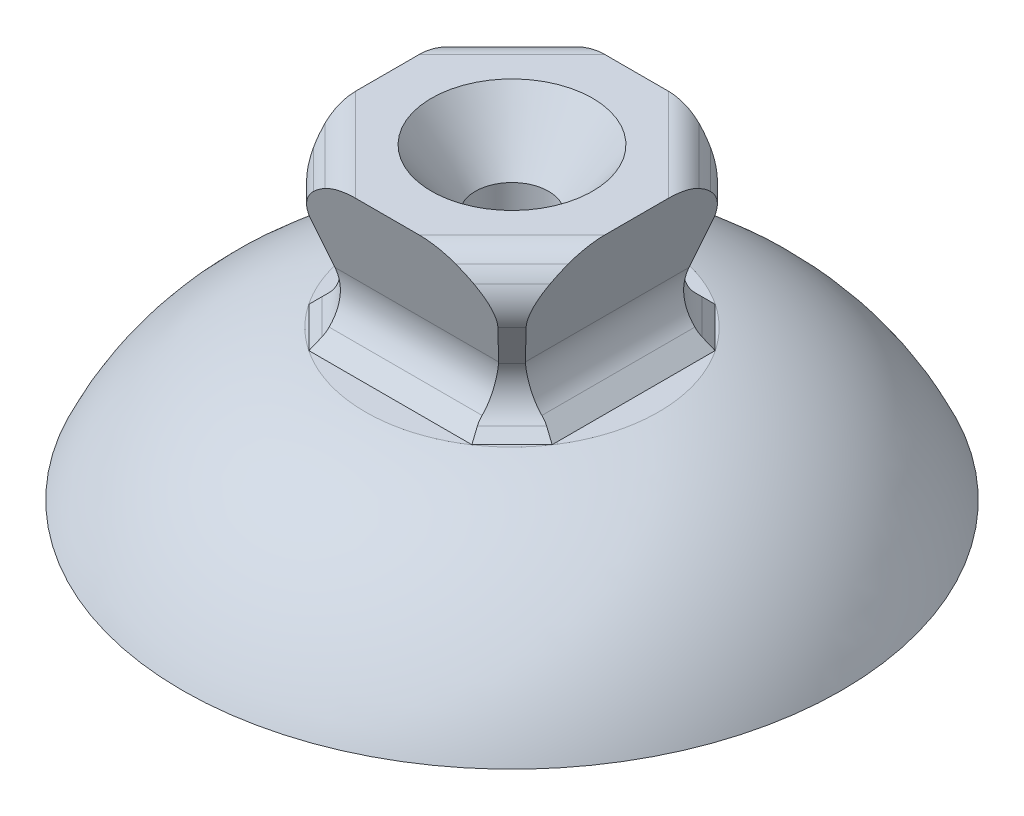
SolidWorks part; units mm, degrees
material "Commercially Pure CP-Ti UNS R50400 (SS)"
ref_plane "Front Plane" through (0, 0, 0) normal (0, 0, 1) x (1, 0, 0)
ref_plane "Top Plane" through (0, 0, 0) normal (0, 1, 0) x (1, 0, 0)
ref_plane "Right Plane" through (0, 0, 0) normal (1, 0, 0) x (0, 0, -1)
sketch "Sketch4" plane through (0, 0, 0) normal (0, 0, 1) x (1, 0, 0)
  line L1 (-8.5, -5.5) -> (8.5, -5.5)
  line L2 (-8.5, -5.5) -> (-8.5, 5.5)
  line L3 (-8.5, 5.5) -> (8.5, 5.5)
  line L4 (8.5, -5.5) -> (8.5, 5.5)
  line L5 (-8.5, -5.5) -> (8.5, 5.5) construction
  line L6 (-8.5, 5.5) -> (8.5, -5.5) construction
  point P0 (0, 0)
  dimension "D1" = 11
  dimension "D2" = 17
extrude "Boss-Extrude2" add sketch "Sketch4" along normal mid plane 17
sketch "Sketch5" plane through (0, 0, 0) normal (1, 0, 0) x (0, 0, -1)
  line L0 (0, -10) -> (0, 10) construction
  line L1 (8.5, 5.5) -> (6.5025, -1.2915)
  line L2 (8.5, -5.5) -> (7.2593, -4.2593)
  line L3 (-8.5, -5.5) -> (-7.2593, -4.2593)
  line L4 (-8.5, 5.5) -> (-6.5025, -1.2915)
  line L5 (-8.5, 5.5) -> (-8.5, -5.5)
  line L6 (8.5, -5.5) -> (8.5, 5.5)
  arc A0 (7.2593, -4.2593) -> (6.5025, -1.2915) centre (9.3806, -2.138) cw
  arc A1 (-7.2593, -4.2593) -> (-6.5025, -1.2915) centre (-9.3806, -2.138) ccw
  point P12 (6, -3)
  point P16 (-6, -3)
  dimension "D5" = 3
  dimension "D1" = 10
  dimension "D2" = 20
  dimension "D3" = 6
  dimension "D4" = 45
extrude "Cut-Extrude1" cut sketch "Sketch5" against normal mid plane 27
sketch "Sketch7" plane through (0, 0, 0) normal (0, 0, 1) x (1, 0, 0)
  line L0 (0, -10) -> (0, 10) construction
  line L1 (8.5, 5.5) -> (6.5025, -1.2915)
  line L2 (8.5, -5.5) -> (7.2593, -4.2593)
  line L3 (-8.5, -5.5) -> (-7.2593, -4.2593)
  line L4 (-8.5, 5.5) -> (-6.5025, -1.2915)
  line L5 (-8.5, 5.5) -> (-8.5, -5.5)
  line L6 (8.5, -5.5) -> (8.5, 5.5)
  line L7 (8.5, -4.2593) -> (8.5, -5.5) construction
  arc A0 (7.2593, -4.2593) -> (6.5025, -1.2915) centre (9.3806, -2.138) cw
  arc A1 (-7.2593, -4.2593) -> (-6.5025, -1.2915) centre (-9.3806, -2.138) ccw
  point P12 (-6, -3)
  point P14 (0, 0)
  point P16 (8.5, -5.4999)
  dimension "D3" = 3
  dimension "D1" = 20
  dimension "D2" = 45
  dimension "D4" = 16.389
extrude "Cut-Extrude2" cut sketch "Sketch7" against normal mid plane 27
sketch "Sketch8" plane through (0, 5.5, 0) normal (0, 1, 0) x (1, 0, 0)
  line L0 (3.5355, 3.5355) -> (-3.5355, -3.5355) construction
  line L1 (-5, 0) -> (5, 0) construction
  line L2 (-3.5355, 3.5355) -> (3.5355, -3.5355) construction
  line L3 (0, 5) -> (0, -5) construction
  dimension "D1" = 10
  dimension "D2" = 10
  dimension "D3" = 10
  dimension "D4" = 45
  dimension "D5" = 45
  dimension "D6" = 10
sketch "Sketch9" plane through (0, 0, 0) normal (0, 1, 0) x (1, 0, 0)
  line L0 (3.5355, 3.5355) -> (-3.5355, -3.5355) construction
  line L1 (-5, 0) -> (5, 0) construction
  line L2 (-3.5355, 3.5355) -> (3.5355, -3.5355) construction
  line L3 (0, 5) -> (0, -5) construction
  point P8 (0, 0)
  point P10 (0, 0)
  point P11 (0, 0)
  dimension "D1" = 10
  dimension "D2" = 10
  dimension "D3" = 10
  dimension "D4" = 45
  dimension "D5" = 45
  dimension "D6" = 10
ref_plane "Plane1" through (0, 0, 0) normal (0.7071, 0, 0.7071) x (0.7071, 0, -0.7071)
ref_plane "Plane2" through (0, 0, 0) normal (0.7071, 0, -0.7071) x (-0.7071, 0, -0.7071)
sketch "Sketch11" plane through (0, 0, 0) normal (0.7071, 0, 0.7071) x (0.7071, 0, -0.7071)
  line L0 (-10, 5.5) -> (10, 5.5) construction
  line L1 (0, -5.5) -> (0, 5.5) construction
  line L2 (10, 5.5) -> (10, -5.5) construction
  line L3 (0, -5.5) -> (12.0208, -5.5) construction
  line L4 (10, -5.5) -> (0, -5.5) construction
  line L5 (10, -5.5) -> (9.1595, -4.6595)
  line L6 (10, 5.5) -> (10, 2.3) construction
  line L7 (0, 5.5) -> (8.25, 5.5) construction
  line L8 (9.6935, 1.5413) -> (8.4993, -1.4144)
  line L10 (10, -5.5) -> (14, -5.5)
  line L11 (14, -5.5) -> (14, 5.5)
  line L12 (14, 5.5) -> (8.25, 5.5)
  line L13 (-14, 5.5) -> (-8.25, 5.5)
  line L14 (-9.6935, 1.5413) -> (-8.4993, -1.4144)
  line L15 (-10, -5.5) -> (-9.1595, -4.6595)
  line L16 (-10, -5.5) -> (-14, -5.5)
  line L17 (-14, -5.5) -> (-14, 5.5)
  arc A0 (9.5819, 4.0331) -> (8.25, 5.5) centre (6.1993, 2.3) ccw
  arc A1 (9.5819, 4.0331) -> (9.6935, 1.5413) centre (6.9119, 2.6651) cw
  arc A2 (9.1595, -4.6595) -> (8.4993, -1.4144) centre (11.2808, -2.5382) cw
  arc A3 (-9.5819, 4.0331) -> (-9.6935, 1.5413) centre (-6.9119, 2.6651) ccw
  arc A4 (-9.5819, 4.0331) -> (-8.25, 5.5) centre (-6.1993, 2.3) cw
  arc A5 (-9.1595, -4.6595) -> (-8.4993, -1.4144) centre (-11.2808, -2.5382) ccw
  dimension "D7" = 3
  dimension "D8" = 3
  dimension "D1" = 20
  dimension "D2" = 11
  dimension "D3" = 45
  dimension "D4" = 8.25
  dimension "D5" = 3.2
  dimension "D6" = 22
  dimension "D9" = 4
extrude "Cut-Extrude3" cut sketch "Sketch11" against normal mid plane 27
sketch "Sketch12" plane through (0, 0, 0) normal (0.7071, 0, -0.7071) x (-0.7071, 0, -0.7071)
  line L0 (-10, 5.5) -> (10, 5.5) construction
  line L1 (0, -5.5) -> (0, 5.5) construction
  line L2 (10, 5.5) -> (10, -5.5) construction
  line L3 (10, -5.5) -> (0, -5.5) construction
  line L4 (10, -5.5) -> (9.1595, -4.6595)
  line L5 (10, 5.5) -> (10, 2.3) construction
  line L6 (0, 5.5) -> (8.25, 5.5) construction
  line L7 (9.6935, 1.5413) -> (8.4993, -1.4144)
  line L8 (10, -5.5) -> (14, -5.5)
  line L9 (14, -5.5) -> (14, 5.5)
  line L10 (14, 5.5) -> (8.25, 5.5)
  line L11 (-14, 5.5) -> (-8.25, 5.5)
  line L12 (-9.6935, 1.5413) -> (-8.4993, -1.4144)
  line L13 (-10, -5.5) -> (-9.1595, -4.6595)
  line L14 (-10, -5.5) -> (-14, -5.5)
  line L15 (-14, -5.5) -> (-14, 5.5)
  arc A0 (9.5819, 4.0331) -> (8.25, 5.5) centre (6.1993, 2.3) ccw
  arc A1 (9.5819, 4.0331) -> (9.6935, 1.5413) centre (6.9119, 2.6651) cw
  arc A2 (9.1595, -4.6595) -> (8.4993, -1.4144) centre (11.2808, -2.5382) cw
  arc A3 (-9.5819, 4.0331) -> (-9.6935, 1.5413) centre (-6.9119, 2.6651) ccw
  arc A4 (-9.5819, 4.0331) -> (-8.25, 5.5) centre (-6.1993, 2.3) cw
  arc A5 (-9.1595, -4.6595) -> (-8.4993, -1.4144) centre (-11.2808, -2.5382) ccw
  point P27 (0, 0)
  dimension "D7" = 3
  dimension "D8" = 3
  dimension "D1" = 20
  dimension "D2" = 11
  dimension "D3" = 45
  dimension "D4" = 8.25
  dimension "D5" = 3.2
  dimension "D6" = 22
  dimension "D9" = 4
extrude "Cut-Extrude4" cut sketch "Sketch12" against normal mid plane 27
sketch "Sketch14" plane through (0, 0, 0) normal (0, 0, 1) x (1, 0, 0)
  line L0 (0, 5.5) -> (0, -5.5) construction
  line L1 (0, 5.5) -> (5.5, 5.5)
  line L2 (3.1673, 5.5) -> (8.5, 5.5) construction
  line L3 (5.5, 5.5) -> (5.5, 1.5) construction
  line L4 (0, 1.5) -> (2.5, 1.5) construction
  line L5 (2.5, 1.5) -> (5.5, 5.5)
  line L6 (2.5, 1.5) -> (2.5, -5.5)
  line L7 (-5.6421, -5.5) -> (5.6421, -5.5) construction
  line L8 (0, -5.5) -> (0, 5.5)
  line L9 (2.5, -5.5) -> (0, -5.5)
  dimension "D1" = 11
  dimension "D2" = 5.5
  dimension "D3" = 4
  dimension "D4" = 2.5
revolve "Cut-Revolve1" cut sketch "Sketch14" angle 360 about L8
fillet "Fillet1" radius 2 4 edges at (5.8336, 5.5, -5.8336) (-5.8336, 5.5, -5.8336) (-5.8336, 5.5, 5.8336) (5.8336, 5.5, 5.8336)
sketch "Sketch15" plane through (0, 0, 0) normal (1, 0, 0) x (0, 0, -1)
  line L0 (0, -5.5) -> (0, -15.5) construction
  line L1 (-5.6421, -5.5) -> (5.6421, -5.5) construction
  line L3 (0, -15.5) -> (22.5, -15.5)
  line L4 (0, -15.5) -> (0, -5.5)
  line L5 (0, -5.5) -> (0, -5.3)
  line L6 (0, -5.3) -> (9.998, -5.3)
  arc A0 (9.998, -5.3) -> (22.5, -15.5) centre (6.077, -22.8677) cw
  point P8 (0, 0)
  dimension "D4" = 18
  dimension "D1" = 10
  dimension "D2" = 10
  dimension "D3" = 22.5
  dimension "D5" = 0.2
revolve "Revolve1" add sketch "Sketch15" angle 360 about L0
